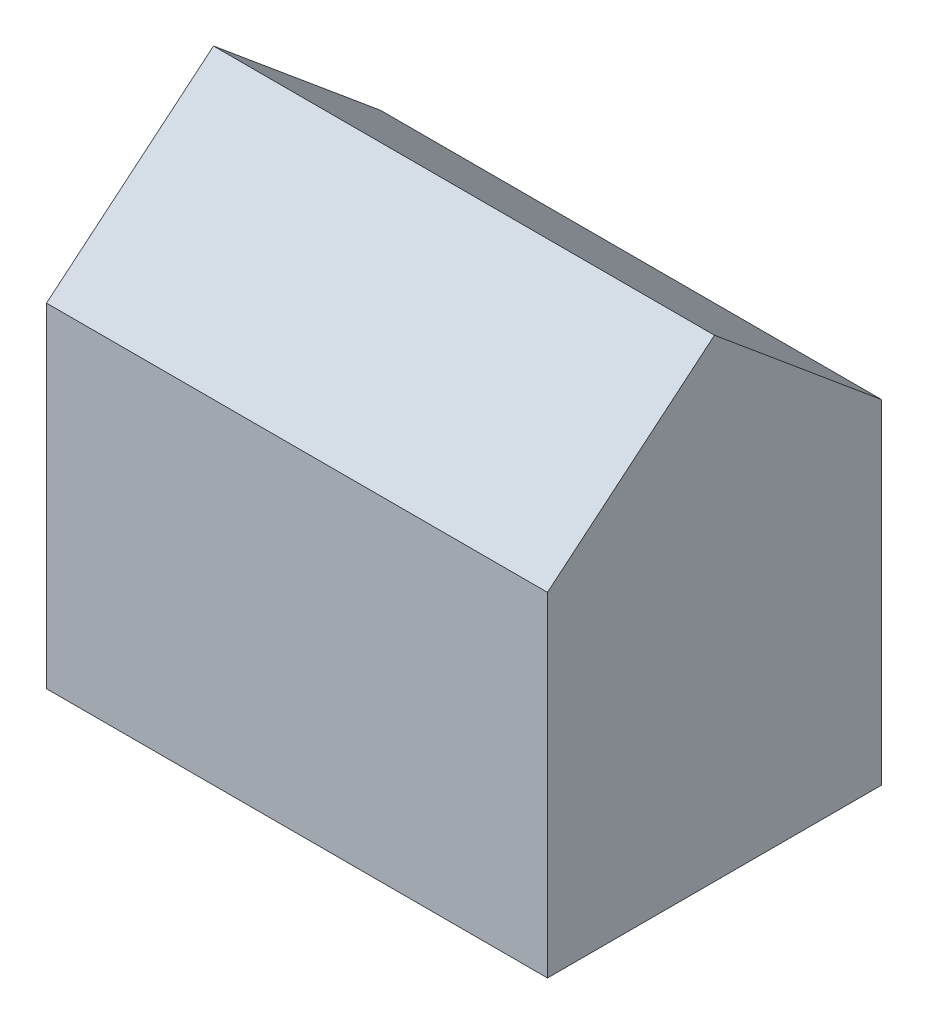
SolidWorks part; units mm, degrees
ref_plane "Front Plane" through (0, 0, 0) normal (0, 0, 1) x (1, 0, 0)
ref_plane "Top Plane" through (0, 0, 0) normal (0, 1, 0) x (1, 0, 0)
ref_plane "Right Plane" through (0, 0, 0) normal (1, 0, 0) x (0, 0, -1)
sketch "Sketch1" plane through (0, 0, 0) normal (0, 1, 0) x (1, 0, 0)
  line L1 (0, 0) -> (18, 0)
  line L2 (0, 0) -> (0, 12)
  line L3 (0, 12) -> (18, 12)
  line L4 (18, 0) -> (18, 12)
  line L5 (2, 2) -> (16, 2)
  line L6 (2, 2) -> (2, 10)
  line L7 (2, 10) -> (16, 10)
  line L8 (16, 2) -> (16, 10)
  dimension "D1" = 18
  dimension "D2" = 12
  dimension "D3" = 2
  dimension "D4" = 2
  dimension "D5" = 2
  dimension "D6" = 2
extrude "Boss-Extrude1" add sketch "Sketch1" along normal blind 12
sketch "Sketch2" plane through (18, 0, 0) normal (1, 0, 0) x (0, 0, -1)
  line L0 (6, 17) -> (0, 12)
  line L1 (6, 17) -> (12, 12)
  line L6 (0, 0) -> (12, 0)
  line L7 (12, 0) -> (12, 12)
  line L8 (12, 12) -> (0, 12)
  line L9 (0, 12) -> (0, 0)
  line L12 (12, 12) -> (0, 12)
  point P7 (6, 12)
  dimension "D1" = 5
  dimension "D2" = 0
extrude "Boss-Extrude2" add sketch "Sketch2" against normal blind 18
